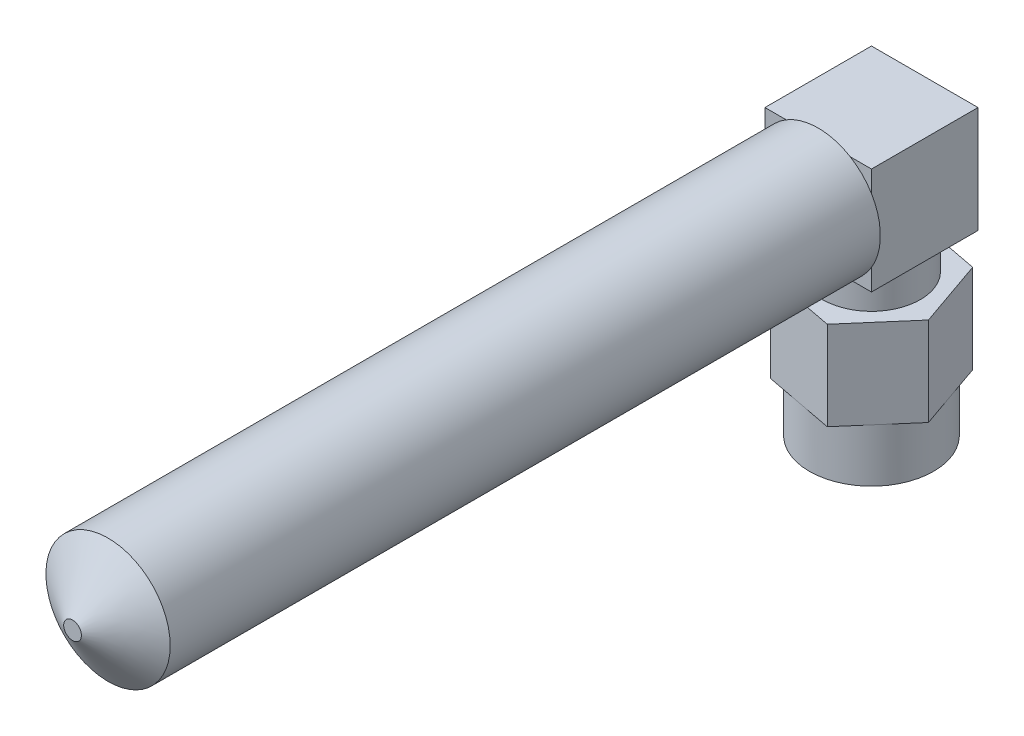
SolidWorks part; units mm, degrees
ref_plane "前视基准面" through (0, 0, 0) normal (0, 0, 1) x (1, 0, 0)
ref_plane "上视基准面" through (0, 0, 0) normal (0, 1, 0) x (1, 0, 0)
ref_plane "右视基准面" through (0, 0, 0) normal (1, 0, 0) x (0, 0, -1)
sketch "草图1" plane through (0, 0, 0) normal (0, 1, 0) x (1, 0, 0)
  circle A0 centre (0, 0) radius 3.5
  dimension "D1" = 7
extrude "凸台-拉伸1" add sketch "草图1" along normal blind 3
sketch "草图2" plane through (0, 3, 0) normal (0, 1, 0) x (1, 0, 0)
  line L1 (2.6427, 3.0577) -> (-1.3267, 3.8175)
  line L2 (-1.3267, 3.8175) -> (-3.9694, 0.7597)
  line L3 (-3.9694, 0.7597) -> (-2.6427, -3.0577)
  line L4 (-2.6427, -3.0577) -> (1.3267, -3.8175)
  line L5 (1.3267, -3.8175) -> (3.9694, -0.7597)
  line L6 (3.9694, -0.7597) -> (2.6427, 3.0577)
  circle A0 centre (0, 0) radius 3.5 construction
  dimension "D1" = 7
extrude "凸台-拉伸2" add sketch "草图2" along normal blind 5
sketch "草图3" plane through (0, 8, 0) normal (0, 1, 0) x (1, 0, 0)
  circle A0 centre (0, 0) radius 2.75
  dimension "D1" = 5.5
extrude "凸台-拉伸3" add sketch "草图3" along normal blind 2
sketch "草图4" plane through (0, 0, 0) normal (0, -1, 0) x (1, 0, 0)
  circle A0 centre (0, 0) radius 2.5
  dimension "D1" = 5
extrude "切除-拉伸1" cut sketch "草图4" against normal blind 5
sketch "草图5" plane through (0, 10, 0) normal (0, 1, 0) x (1, 0, 0)
  line L1 (3, -3) -> (-3, -3)
  line L2 (3, -3) -> (3, 3)
  line L3 (3, 3) -> (-3, 3)
  line L4 (-3, -3) -> (-3, 3)
  line L5 (0, 3) -> (0, -3) construction
  line L6 (3, 0) -> (-3, 0) construction
  point P0 (0, 0)
  dimension "D1" = 6
  dimension "D2" = 6
extrude "凸台-拉伸4" add sketch "草图5" along normal blind 6
sketch "草图6" plane through (0, 0, 3) normal (0, 0, 1) x (1, 0, 0)
  circle A0 centre (0, 13) radius 3.5
  dimension "D1" = 7
extrude "凸台-拉伸7" add sketch "草图6" along normal blind 40
ref_axis "基准轴1" through (0, 13, 43) along (0, 0, -1)
sketch "草图7" plane through (0, 0, 0) normal (1, 0, 0) x (0, 0, -1)
  line L0 (-43, 16.5) -> (-43, 13)
  line L1 (-43, 16.5) -> (-43, 9.5) construction
  line L2 (-43, 13) -> (-45, 13)
  line L3 (-45, 13) -> (-45, 13.5)
  line L4 (-45, 13.5) -> (-43, 16.5)
  dimension "D1" = 2
  dimension "D2" = 0.5
revolve "旋转1" add sketch "草图7" angle 360 about axis through (0, 13, 43) along (0, 0, -1)
